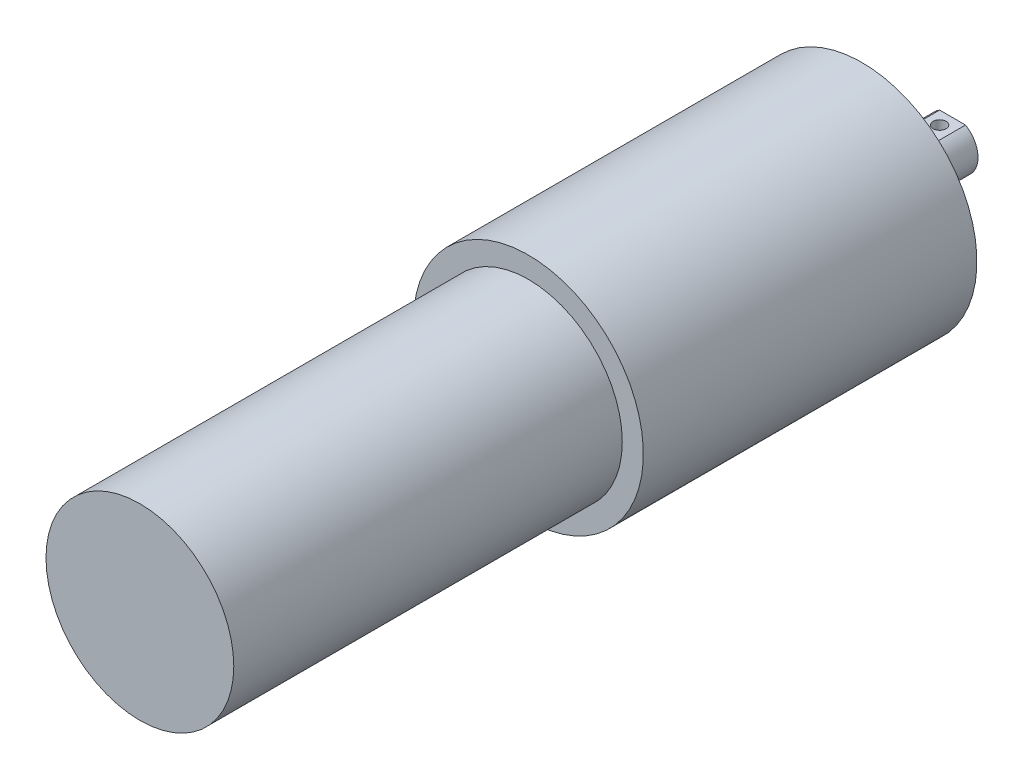
SolidWorks part; units mm, degrees
ref_plane "Front" through (0, 0, 0) normal (0, 0, 1) x (1, 0, 0)
ref_plane "Top" through (0, 0, 0) normal (0, 1, 0) x (1, 0, 0)
ref_plane "Right" through (0, 0, 0) normal (1, 0, 0) x (0, 0, -1)
sketch "Sketch1" plane through (0, 0, 0) normal (0, 0, 1) x (1, 0, 0)
  circle A0 centre (0, 0) radius 18.415
  dimension "D1" = 36.83
extrude "Boss-Extrude1" add sketch "Sketch1" along normal blind 76.2
sketch "Sketch2" plane through (0, 0, 0) normal (0, 0, -1) x (-1, 0, 0)
  circle A0 centre (0, 0) radius 22.5489
  dimension "D1" = 45.0977
extrude "Boss-Extrude2" add sketch "Sketch2" along normal blind 65.4177
sketch "Sketch3" plane through (0, 0, -65.4177) normal (0, 0, -1) x (-1, 0, 0)
  circle A0 centre (0, 0) radius 4.9911
  dimension "D1" = 9.9822
extrude "Boss-Extrude3" add sketch "Sketch3" along normal blind 17.78
sketch "Sketch5" plane through (0, 0, -83.1977) normal (0, 0, -1) x (-1, 0, 0)
  line L0 (0, 4.2964) -> (0, 0) construction
  line L1 (-2.54, 5.5502) -> (2.54, 5.5502)
  line L2 (-2.54, 5.5502) -> (-2.54, 4.2964)
  line L3 (-2.54, 4.2964) -> (2.54, 4.2964)
  line L4 (2.54, 5.5502) -> (2.54, 4.2964)
  circle A0 centre (0, 0) radius 4.9911 construction
  dimension "D1" = 5.08
extrude "Cut-Extrude1" cut sketch "Sketch5" against normal blind 7.62
sketch "Sketch6" plane through (0, 4.2964, 0) normal (0, 1, 0) x (1, 0, 0)
  line L0 (-2.54, 75.5777) -> (-2.54, 83.1977) construction
  line L1 (2.54, 83.1977) -> (-2.54, 83.1977) construction
  circle A0 centre (0, 80.6577) radius 1.27
  dimension "D1" = 2.54
  dimension "D2" = 2.54
  dimension "D3" = 2.54
extrude "Cut-Extrude2" cut sketch "Sketch6" against normal up to next
